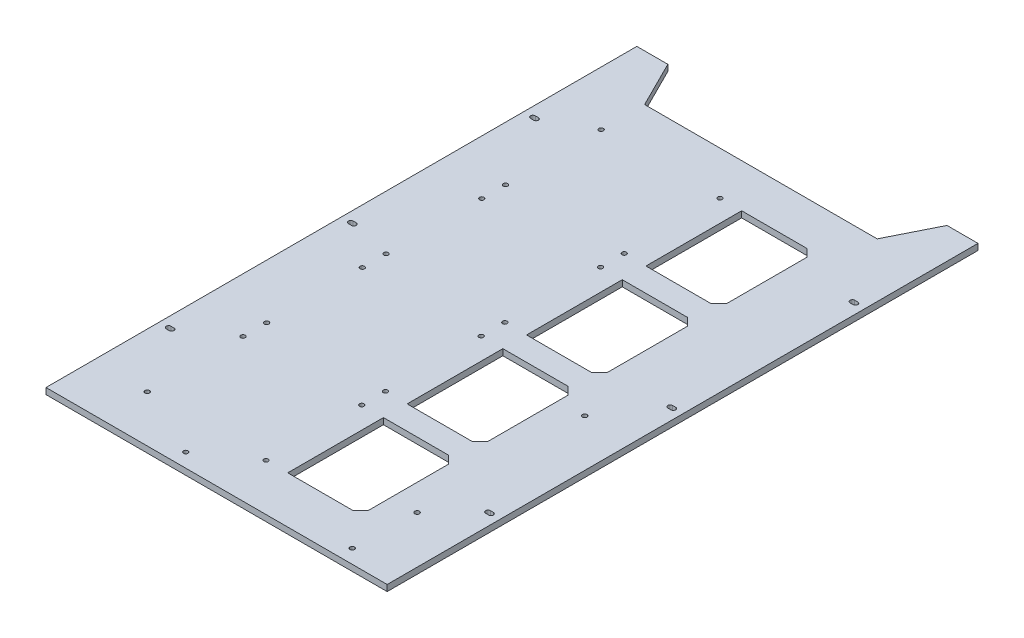
SolidWorks part; units mm, degrees
ref_plane "前基準面" through (0, 0, 0) normal (0, 0, 1) x (1, 0, 0)
ref_plane "上基準面" through (0, 0, 0) normal (0, 1, 0) x (1, 0, 0)
ref_plane "右基準面" through (0, 0, 0) normal (1, 0, 0) x (0, 0, -1)
ref_plane "平面1" through (0, 4, 0) normal (0, 1, 0) x (1, 0, 0)
sketch "草圖1" plane through (0, 4, 0) normal (0, 1, 0) x (1, 0, 0)
  line L0 (-75, 160.5) -> (-90, 190.5)
  line L1 (-90, 190.5) -> (-110, 190.5)
  line L2 (-110, 190.5) -> (-110, -190.5)
  line L3 (-110, -190.5) -> (110, -190.5)
  line L4 (110, -190.5) -> (110, 190.5)
  line L5 (110, 190.5) -> (90, 190.5)
  line L6 (90, 190.5) -> (75, 160.5)
  line L7 (75, 160.5) -> (-75, 160.5)
  line L8 (-104, 1.5) -> (-102, 1.5)
  line L9 (-102, -1.5) -> (-104, -1.5)
  line L10 (102, -116) -> (104, -116)
  line L11 (104, -119) -> (102, -119)
  line L12 (102, 1.5) -> (104, 1.5)
  line L13 (104, -1.5) -> (102, -1.5)
  line L14 (102, 119) -> (104, 119)
  line L15 (104, 116) -> (102, 116)
  line L16 (-104, -116) -> (-102, -116)
  line L17 (-102, -119) -> (-104, -119)
  line L18 (-104, 119) -> (-102, 119)
  line L19 (-102, 116) -> (-104, 116)
  line L20 (15.6, 132.5) -> (57.6, 132.5)
  line L21 (57.6, 132.5) -> (62.6, 127.5)
  line L22 (62.6, 127.5) -> (62.6, 75.78)
  line L23 (62.6, 75.78) -> (57.6, 70.78)
  line L24 (57.6, 70.78) -> (15.6, 70.78)
  line L25 (15.6, 70.78) -> (15.6, 132.5)
  line L26 (57.6, 55.5) -> (62.6, 50.5)
  line L27 (62.6, 50.5) -> (62.6, -1.22)
  line L28 (62.6, -1.22) -> (57.6, -6.22)
  line L29 (57.6, -6.22) -> (15.6, -6.22)
  line L30 (15.6, -6.22) -> (15.6, 55.5)
  line L31 (15.6, 55.5) -> (57.6, 55.5)
  line L32 (57.6, -21.5) -> (62.6, -26.5)
  line L33 (62.6, -26.5) -> (62.6, -78.22)
  line L34 (62.6, -78.22) -> (57.6, -83.22)
  line L35 (57.6, -83.22) -> (15.6, -83.22)
  line L36 (15.6, -83.22) -> (15.6, -21.5)
  line L37 (15.6, -21.5) -> (57.6, -21.5)
  line L38 (57.6, -98.5) -> (62.6, -103.5)
  line L39 (62.6, -103.5) -> (62.6, -155.22)
  line L40 (62.6, -155.22) -> (57.6, -160.22)
  line L41 (57.6, -160.22) -> (15.6, -160.22)
  line L42 (15.6, -160.22) -> (15.6, -98.5)
  line L43 (15.6, -98.5) -> (57.6, -98.5)
  arc A0 (-102, 1.5) -> (-102, -1.5) centre (-102, 0) cw
  arc A1 (-104, -1.5) -> (-104, 1.5) centre (-104, 0) cw
  arc A2 (104, -116) -> (104, -119) centre (104, -117.5) cw
  arc A3 (102, -119) -> (102, -116) centre (102, -117.5) cw
  arc A4 (104, 1.5) -> (104, -1.5) centre (104, 0) cw
  arc A5 (102, -1.5) -> (102, 1.5) centre (102, 0) cw
  arc A6 (104, 119) -> (104, 116) centre (104, 117.5) cw
  arc A7 (102, 116) -> (102, 119) centre (102, 117.5) cw
  arc A8 (-102, -116) -> (-102, -119) centre (-102, -117.5) cw
  arc A9 (-104, -119) -> (-104, -116) centre (-104, -117.5) cw
  arc A10 (-102, 119) -> (-102, 116) centre (-102, 117.5) cw
  arc A11 (-104, 116) -> (-104, 119) centre (-104, 117.5) cw
  circle A12 centre (79.5, -32.625) radius 1.5
  circle A13 centre (79.5, -140.625) radius 1.5
  circle A14 centre (-75, 132.5) radius 1.45
  circle A15 centre (1.6, 132.5) radius 1.45
  circle A16 centre (-75, 70.78) radius 1.45
  circle A17 centre (1.6, 70.78) radius 1.45
  circle A18 centre (1.6, 55.5) radius 1.45
  circle A19 centre (-75, 55.5) radius 1.45
  circle A20 centre (-75, -6.22) radius 1.45
  circle A21 centre (1.6, -6.22) radius 1.45
  circle A22 centre (-75, -21.5) radius 1.45
  circle A23 centre (1.6, -21.5) radius 1.45
  circle A24 centre (-75, -83.22) radius 1.45
  circle A25 centre (1.6, -83.22) radius 1.45
  circle A26 centre (1.6, -98.5) radius 1.45
  circle A27 centre (-75, -98.5) radius 1.45
  circle A28 centre (-75, -160.22) radius 1.45
  circle A29 centre (1.6, -160.22) radius 1.45
  circle A30 centre (-28.86, -181.5) radius 1.45
  circle A31 centre (78.5, -181.5) radius 1.45
extrude "填料-伸長1" add sketch "草圖1" against normal blind 4
